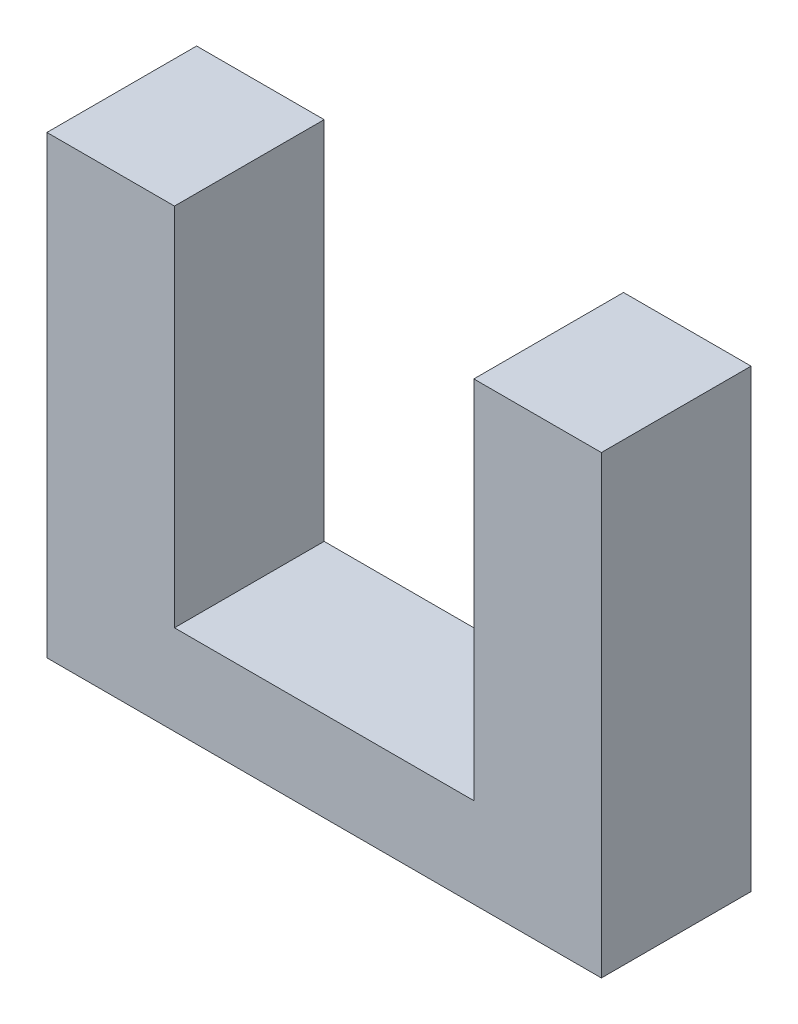
SolidWorks part; units mm, degrees
ref_plane "Front Plane" through (0, 0, 0) normal (0, 0, 1) x (1, 0, 0)
ref_plane "Top Plane" through (0, 0, 0) normal (0, 1, 0) x (1, 0, 0)
ref_plane "Right Plane" through (0, 0, 0) normal (1, 0, 0) x (0, 0, -1)
sketch "Sketch1" plane through (0, 0, 0) normal (0, 0, 1) x (1, 0, 0)
  line L0 (-9.26, -3) -> (-9.26, 12.2)
  line L1 (-9.26, 12.2) -> (-5, 12.2)
  line L2 (-5, 12.2) -> (-5, 0)
  line L3 (-5, 0) -> (5, 0)
  line L4 (5, 0) -> (5, 12.2)
  line L5 (5, 12.2) -> (9.26, 12.2)
  line L6 (9.26, 12.2) -> (9.26, -3)
  line L7 (9.26, -3) -> (-9.26, -3)
  line L8 (0, 0) -> (0, -3) construction
  point P11 (0, 0)
  point P12 (-9.5728, -3.6744)
  point P13 (0, 0)
  dimension "D1" = 18.52
  dimension "D2" = 10
  dimension "D3" = 3
  dimension "D4" = 15.2
extrude "Boss-Extrude1" add sketch "Sketch1" along normal mid plane 5
sketch "Sketch2" plane through (0, -3, 0) normal (0, -1, 0) x (1, 0, 0)
  line L0 (0, 2.5) -> (0, -2.5) construction
  line L1 (-9.26, 2.5) -> (9.26, 2.5) construction
  line L2 (-9.26, -2.5) -> (9.26, -2.5) construction
  circle A0 centre (0, 0) radius 0.715
  point P8 (9.26, 0)
  dimension "D1" = 1.43
extrude "Boss-Extrude2" add sketch "Sketch2" along normal blind 1.3
